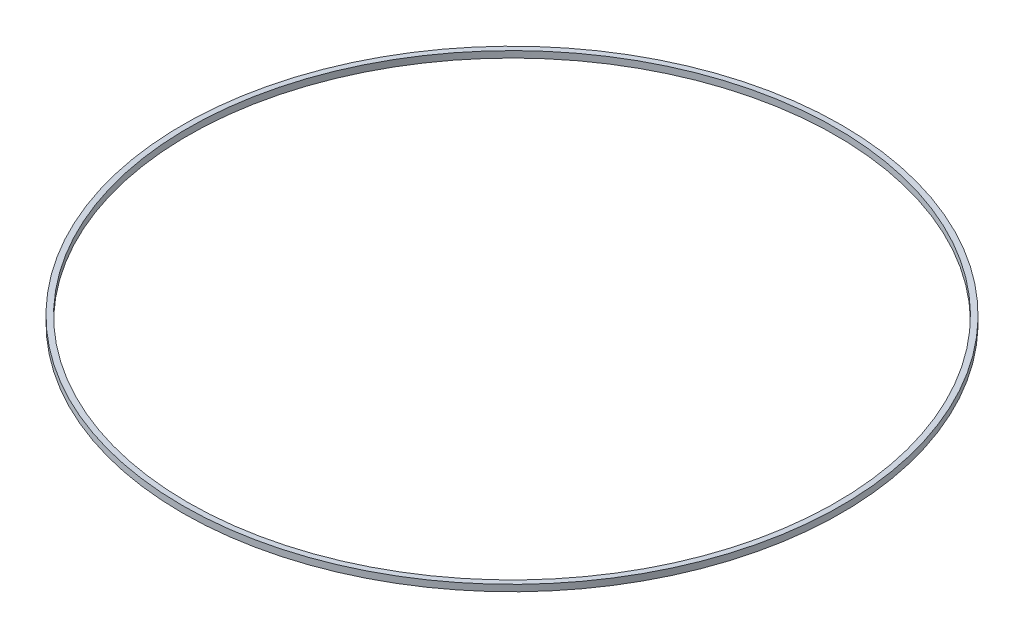
SolidWorks part; units mm, degrees
ref_plane "Front Plane" through (0, 0, 0) normal (0, 0, 1) x (1, 0, 0)
ref_plane "Top Plane" through (0, 0, 0) normal (0, 1, 0) x (1, 0, 0)
ref_plane "Right Plane" through (0, 0, 0) normal (1, 0, 0) x (0, 0, -1)
sketch "Sketch2" plane through (0, 0, 0) normal (0, 1, 0) x (1, 0, 0)
  circle A0 centre (0, 0) radius 153
  circle A1 centre (0, 0) radius 150.5
  dimension "D1" = 306
  dimension "D2" = 301
extrude "Boss-Extrude1" add sketch "Sketch2" along normal blind 3
